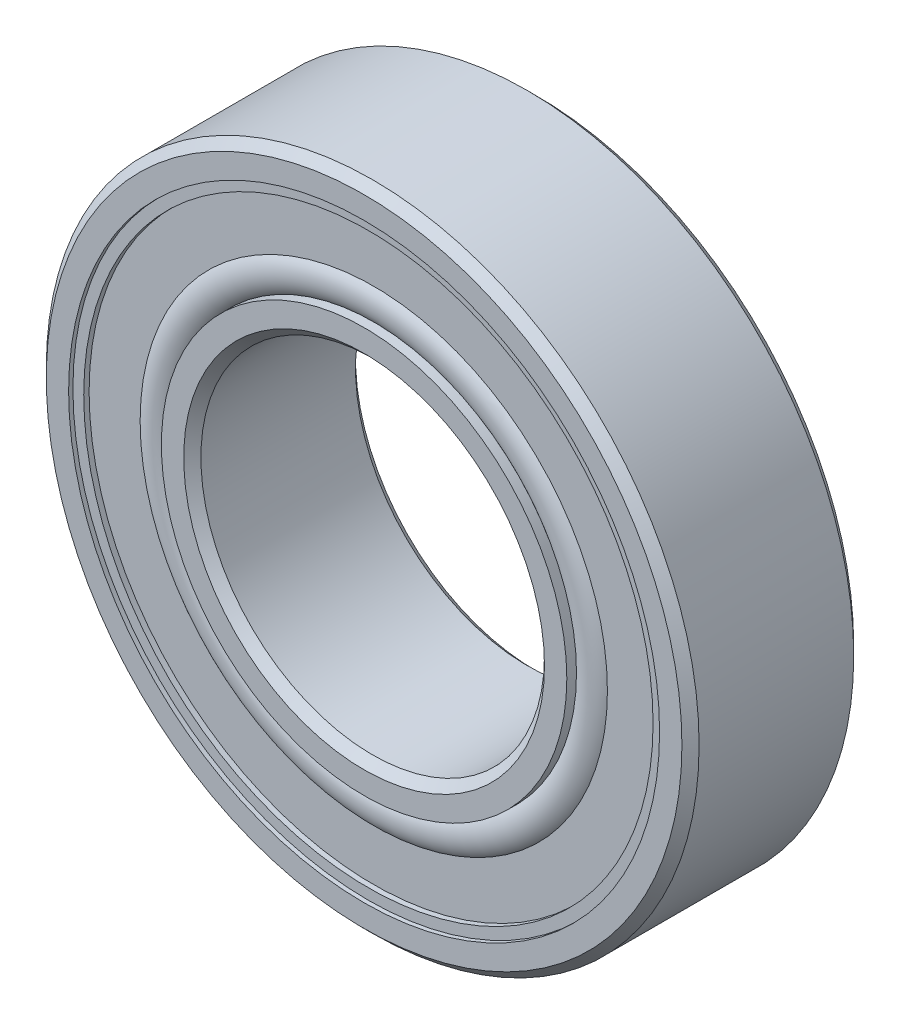
SolidWorks part; units mm, degrees
ref_plane "Front Plane" through (0, 0, 0) normal (0, 0, 1) x (1, 0, 0)
ref_plane "Top Plane" through (0, 0, 0) normal (0, 1, 0) x (1, 0, 0)
ref_plane "Right Plane" through (0, 0, 0) normal (1, 0, 0) x (0, 0, -1)
sketch "Sketch1" plane through (0, 0, 0) normal (0, 0, 1) x (1, 0, 0)
  circle A0 centre (0, 0) radius 9.5 construction
  circle A1 centre (0, 0) radius 5 construction
  dimension "OD" = 19
  dimension "ID" = 10
sketch "Sketch2" plane through (0, 0, 0) normal (1, 0, 0) x (0, 0, -1)
  line L0 (-2.5, 0) -> (2.5, 0) construction
  line L1 (0, 9.5) -> (0, -9.5) construction
  line L2 (2.25, 9.5) -> (-2.25, 9.5) construction
  line L3 (-2.25, 9.5) -> (-2.5, 9.25) construction
  line L4 (-2.5, 9.25) -> (-2.5, 8.6) construction
  line L5 (-2.5, 8.6) -> (-1.1111, 8.6) construction
  line L6 (2.5, 8.6) -> (1.1111, 8.6) construction
  line L7 (2.5, 9.25) -> (2.5, 8.6) construction
  line L8 (2.25, 9.5) -> (2.5, 9.25) construction
  line L9 (0, 9.5) -> (0, 7.25) construction
  line L10 (0, 7.25) -> (0, 5) construction
  line L11 (2.5, 7.25) -> (-2.5, 7.25) construction
  line L12 (-2.5, 5.25) -> (-2.5, 5.9) construction
  line L13 (-2.25, 5) -> (-2.5, 5.25) construction
  line L14 (2.25, 5) -> (-2.25, 5) construction
  line L15 (2.25, 5) -> (2.5, 5.25) construction
  line L16 (2.5, 5.25) -> (2.5, 5.9) construction
  line L17 (2.5, 5.9) -> (1.1111, 5.9) construction
  line L18 (-2.5, 5.9) -> (-1.1111, 5.9) construction
  line L19 (-2.5, 5) -> (-2.5, -5) construction
  line L20 (2.5, 9.5) -> (2.5, -9.5) construction
  arc A0 (-1.1111, 8.6) -> (1.1111, 8.6) centre (0, 7.25) cw construction
  arc A1 (-1.1111, 5.9) -> (1.1111, 5.9) centre (0, 7.25) ccw construction
  point P14 (0, 5)
  point P18 (0, 7.25)
  dimension "Approx. Ball Dia." = 3.4969
  dimension "D1" = 45
  dimension "D2" = 0.25
  dimension "D3" = 2.2222
  dimension "D4" = 1.35
  dimension "Width" = 5
  dimension "For Shaft Diameter" = 10
  dimension "For Housing ID" = 19
sketch "Sketch3" plane through (0, 0, 0) normal (1, 0, 0) x (0, 0, -1)
  line L0 (-2.5, 9.25) -> (-2.5, 8.6) construction
  line L1 (-2.25, 9.5) -> (-2.5, 9.25) construction
  line L2 (2.25, 9.5) -> (-2.25, 9.5) construction
  line L3 (2.25, 9.5) -> (2.5, 9.25) construction
  line L4 (2.5, 9.25) -> (2.5, 8.6) construction
  line L5 (2.5, 8.6) -> (1.1111, 8.6) construction
  line L6 (-2.5, 8.6) -> (-1.1111, 8.6) construction
  line L7 (-2.5, 9.25) -> (-2.5, 8.6)
  line L8 (-2.25, 9.5) -> (-2.5, 9.25)
  line L9 (2.25, 9.5) -> (-2.25, 9.5)
  line L10 (2.25, 9.5) -> (2.5, 9.25)
  line L11 (2.5, 9.25) -> (2.5, 8.6)
  line L12 (2.5, 8.6) -> (1.1111, 8.6)
  line L13 (-2.5, 8.6) -> (-1.1111, 8.6)
  line L14 (-2.5, 5.25) -> (-2.5, 5.9) construction
  line L15 (-2.25, 5) -> (-2.5, 5.25) construction
  line L16 (2.25, 5) -> (-2.25, 5) construction
  line L17 (2.25, 5) -> (2.5, 5.25) construction
  line L18 (2.5, 5.25) -> (2.5, 5.9) construction
  line L19 (2.5, 5.9) -> (1.1111, 5.9) construction
  line L20 (-2.5, 5.9) -> (-1.1111, 5.9) construction
  line L21 (-2.5, 5.25) -> (-2.5, 5.9)
  line L22 (-2.25, 5) -> (-2.5, 5.25)
  line L23 (2.25, 5) -> (-2.25, 5)
  line L24 (2.25, 5) -> (2.5, 5.25)
  line L25 (2.5, 5.25) -> (2.5, 5.9)
  line L26 (2.5, 5.9) -> (1.1111, 5.9)
  line L27 (-2.5, 5.9) -> (-1.1111, 5.9)
  arc A0 (1.1111, 8.6) -> (-1.1111, 8.6) centre (0, 7.25) ccw construction
  arc A1 (1.1111, 8.6) -> (-1.1111, 8.6) centre (0, 7.25) ccw
  arc A2 (-1.1111, 5.9) -> (1.1111, 5.9) centre (0, 7.25) ccw construction
  arc A3 (-1.1111, 5.9) -> (1.1111, 5.9) centre (0, 7.25) ccw
revolve "Revolve1" add sketch "Sketch3" angle 360 about L0
sketch "Sketch4" plane through (0, 0, 0) normal (1, 0, 0) x (0, 0, -1)
  line L0 (-1.7484, 7.25) -> (1.7484, 7.25)
  arc A2 (-1.7484, 7.25) -> (1.7484, 7.25) centre (0, 7.25) cw
  arc A3 (1.1111, 8.6) -> (-1.1111, 8.6) centre (0, 7.25) ccw construction
revolve "Revolve2" add sketch "Sketch4" angle 360 about L0
pattern_circular "CirPattern1" count 9 over 360 about axis through (0, 0, 0) along (0, 0, 1) of bodies 104
sketch "Sketch5" plane through (0, 0, 0) normal (1, 0, 0) x (0, 0, -1)
  line L0 (-2.5, 8.6) -> (-1.1111, 8.6) construction
  line L1 (-2.375, 8.6) -> (-1.7484, 8.6)
  line L2 (-2.375, 8.6) -> (-2.375, 8.285)
  line L3 (-2.375, 5.9) -> (-1.7484, 5.9) construction
  line L4 (-1.7484, 8.6) -> (-1.7484, 5.9)
  line L5 (0, 9.5) -> (0, 0) construction
  line L7 (-2.375, 8.285) -> (-2.2184, 8.285)
  line L8 (-2.2184, 8.285) -> (-2.2184, 6.8)
  line L9 (-2.2184, 6.8) -> (-2.375, 6.8) construction
  line L10 (-2.375, 6.8) -> (-2.375, 5.9) construction
  line L11 (2.25, 9.5) -> (-2.25, 9.5) construction
  line L12 (-2.25, 9.5) -> (-2.5, 9.25) construction
  line L13 (-2.5, 5.9) -> (-1.1111, 5.9) construction
  line L15 (-2.2184, 5.9) -> (-1.7484, 5.9)
  line L16 (2.375, 6.8) -> (2.375, 5.9) construction
  line L17 (2.2184, 6.8) -> (2.375, 6.8) construction
  line L18 (2.375, 5.9) -> (1.7484, 5.9) construction
  line L19 (2.2184, 5.9) -> (1.7484, 5.9)
  line L20 (2.2184, 8.285) -> (2.2184, 6.8)
  line L21 (2.375, 8.285) -> (2.2184, 8.285)
  line L22 (1.7484, 8.6) -> (1.7484, 5.9)
  line L23 (2.375, 8.6) -> (2.375, 8.285)
  line L24 (2.375, 8.6) -> (1.7484, 8.6)
  arc A0 (-2.2184, 5.9) -> (-2.2184, 6.8) centre (-1.6503, 6.35) cw
  arc A1 (2.2184, 5.9) -> (2.2184, 6.8) centre (1.6503, 6.35) ccw
  point P10 (-2.2184, 5.9)
  point P18 (-2.375, 9.375)
  dimension "D1" = 0.315
  dimension "D2" = 0.9
  dimension "D3" = 0.6266
  dimension "D4" = 0.1566
revolve "Revolve3" add sketch "Sketch5" angle 360 about L0
equation "\"D2@Sketch2\"= \"Width@Sketch2\" * .05"
equation "\"D3@Sketch2\"=\"Width@Sketch2\" / 2.25"
equation "\"D4@Sketch2\"=( \"OD@Sketch1\" - \"For Shaft Diameter@Sketch2\" ) *0.15"
equation "\"Approx. No. of Balls\"= ( pi * \"OD@Sketch1\" ) * .5 / \"Approx. Ball Dia.@Sketch2\""
equation "\"Balls@CirPattern1\"=\"Approx. No. of Balls\""
equation "\"D1@Sketch5\"=( \"OD@Sketch1\" - \"For Shaft Diameter@Sketch2\" ) *0.035"
equation "\"D2@Sketch5\"=( \"OD@Sketch1\" - \"For Shaft Diameter@Sketch2\" ) *0.1"
equation "\"D4@Sketch5\"=\"D3@Sketch5\"*.25"
